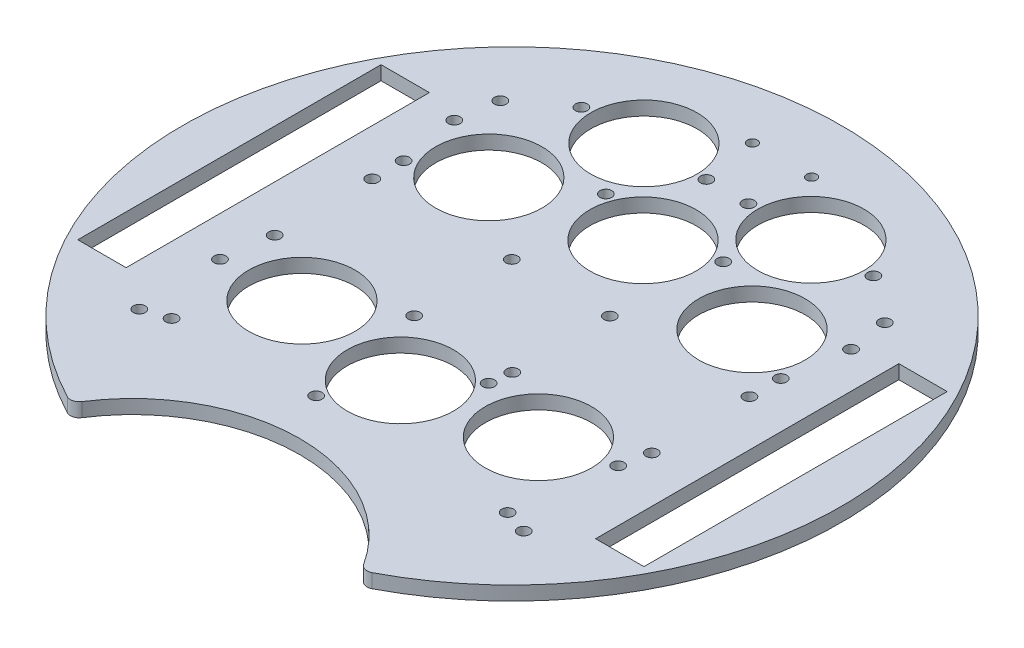
SolidWorks part; units mm, degrees
ref_plane "Front Plane" through (0, 0, 0) normal (0, 0, 1) x (1, 0, 0)
ref_plane "Top Plane" through (0, 0, 0) normal (0, 1, 0) x (1, 0, 0)
ref_plane "Right Plane" through (0, 0, 0) normal (1, 0, 0) x (0, 0, -1)
sketch "Sketch1" plane through (0, 0, 0) normal (0, 1, 0) x (1, 0, 0)
  line L0 (0, 0) -> (-43.7357, 41.0754) construction
  line L1 (0, 86.2583) -> (0, -96.8543) construction
  line L3 (-32.9956, -67.352) -> (0, -86.402) construction
  line L4 (32.9956, -67.352) -> (0, -86.402) construction
  line L5 (0, 0) -> (-13.6167, -50.8184) construction
  line L6 (55.5325, -36.9707) -> (45.152, -29.4289) construction
  line L7 (0, 0) -> (-48.2091, 57.4533) construction
  line L8 (-83.3992, 0) -> (107.0959, 0) construction
  line L9 (53.4101, -34.3971) -> (53.4101, 34.6029)
  line L10 (-64.4101, -34.3971) -> (-53.4101, -34.3971)
  line L11 (-64.4101, -34.3971) -> (-64.4101, 34.6029)
  line L12 (-64.4101, 34.6029) -> (-53.4101, 34.6029)
  line L13 (-53.4101, -34.3971) -> (-53.4101, 34.6029)
  line L14 (64.4101, 34.6029) -> (53.4101, 34.6029)
  line L15 (64.4101, -34.3971) -> (64.4101, 34.6029)
  line L16 (64.4101, -34.3971) -> (53.4101, -34.3971)
  line L17 (0, 0) -> (13.6167, -50.8184) construction
  line L18 (41.9192, -33.8784) -> (45.152, -29.4289) construction
  line L19 (0, 0) -> (48.2091, 57.4533) construction
  line L20 (52.2843, -41.4268) -> (41.9192, -33.8784) construction
  line L21 (64.9519, -37.5) -> (0, 0) construction
  line L22 (28.5723, -45.8735) -> (34.7503, -57.019) construction
  line L23 (28.5723, -45.8735) -> (23.7619, -48.54) construction
  line L24 (44.9916, 49.3407) -> (36.7843, 39.5596) construction
  line L25 (32.5711, 43.0949) -> (36.7843, 39.5596) construction
  line L26 (23.7619, -48.54) -> (29.9399, -59.6854) construction
  line L27 (-28.5723, -45.8735) -> (-34.7503, -57.019) construction
  line L28 (-23.7619, -48.54) -> (-29.9399, -59.6854) construction
  line L29 (-18.4555, -45.8919) -> (-23.0541, -33.9225) construction
  line L30 (-23.0541, -33.9225) -> (-17.92, -31.9499) construction
  line L31 (-28.5723, -45.8735) -> (-23.7619, -48.54) construction
  line L32 (-40.7784, 52.876) -> (-32.5711, 43.0949) construction
  line L33 (-32.5711, 43.0949) -> (-36.7843, 39.5596) construction
  line L34 (40.7784, 52.876) -> (32.5711, 43.0949) construction
  line L35 (-13.6167, -50.8184) -> (-25.1096, -20.9046) construction
  line L36 (-44.9916, 49.3407) -> (-36.7843, 39.5596) construction
  line L37 (-13.3214, -43.9193) -> (-17.92, -31.9499) construction
  line L38 (13.6167, -50.8184) -> (24.3327, -22.8079) construction
  line L39 (18.4555, -45.8919) -> (23.0541, -33.9225) construction
  line L40 (23.0541, -33.9225) -> (17.92, -31.9499) construction
  line L41 (13.3214, -43.9193) -> (17.92, -31.9499) construction
  line L42 (-58.5537, 0) -> (91.2411, 0) construction
  line L43 (-55.5325, -36.9707) -> (-45.152, -29.4289) construction
  line L44 (-52.2843, -41.4268) -> (-41.9192, -33.8784) construction
  line L45 (-41.9192, -33.8784) -> (-45.152, -29.4289) construction
  line L46 (0, 34.6626) -> (0, -51.647) construction
  line L47 (-37.1849, 0) -> (48.113, 0) construction
  line L48 (0, 49.2959) -> (0, -33.0158) construction
  line L54 (8.45, 45.0502) -> (-8.45, 71.1502) construction
  line L55 (8.45, 71.1502) -> (-8.45, 45.0502) construction
  arc A0 (32.9956, -67.352) -> (-32.9956, -67.352) centre (0, 0) ccw
  arc A1 (32.9956, -67.352) -> (-32.9956, -67.352) centre (0, -86.402) ccw
  circle A2 centre (0, 0) radius 74 construction
  arc A3 (56.3744, 49.4664) -> (44.9543, 49.2959) centre (50.737, 44.5198) ccw construction
  arc A4 (-56.3744, 49.4664) -> (-44.9543, 49.2959) centre (-50.737, 44.5198) cw construction
  arc A5 (-45.9, -59.3143) -> (-34.7503, -57.019) centre (-41.31, -53.3829) ccw construction
  arc A6 (45.9, -59.3143) -> (34.7503, -57.019) centre (41.31, -53.3829) cw construction
  arc A7 (-38.9256, 64.1077) -> (-40.7407, 52.8315) centre (-35.033, 57.6969) ccw construction
  arc A8 (-25.9781, -70.3572) -> (-29.9399, -59.6854) centre (-23.3803, -63.3215) cw construction
  arc A9 (25.9781, -70.3572) -> (29.9399, -59.6854) centre (23.3803, -63.3215) ccw construction
  arc A10 (38.9256, 64.1077) -> (40.7407, 52.8315) centre (35.033, 57.6969) cw construction
  arc A11 (53.2525, -52.8127) -> (52.2843, -41.4268) centre (47.9272, -47.5314) ccw construction
  arc A12 (66.658, -34.376) -> (55.5325, -36.9707) centre (59.9914, -30.9401) cw construction
  arc A13 (-5.2684, -48.6449) -> (-13.3214, -43.9193) centre (-6.3241, -41.2196) cw construction
  arc A14 (-21.2728, -54.7938) -> (-18.4555, -45.8919) centre (-25.4604, -48.5717) ccw construction
  arc A15 (-66.658, -34.376) -> (-55.5325, -36.9707) centre (-59.9914, -30.9401) ccw construction
  arc A16 (-53.2525, -52.8127) -> (-52.2843, -41.4268) centre (-47.9272, -47.5314) cw construction
  arc A17 (21.2728, -54.7938) -> (18.4555, -45.8919) centre (25.4604, -48.5717) cw construction
  arc A18 (5.2684, -48.6449) -> (13.3214, -43.9193) centre (6.3241, -41.2196) ccw construction
  circle A19 centre (-42.9101, 11.1) radius 1.35
  circle A20 centre (-42.9101, -11.1) radius 1.35
  circle A21 centre (-11.1601, -11.1) radius 1.35
  circle A22 centre (-11.1601, 11.1) radius 1.35
  circle A23 centre (11.1601, 11.1) radius 1.35
  circle A24 centre (11.1601, -11.1) radius 1.35
  circle A25 centre (42.9101, -11.1) radius 1.35
  circle A26 centre (42.9101, 11.1) radius 1.35
  circle A27 centre (26.9058, -20.9046) radius 12.095
  circle A28 centre (19, 49) radius 12.095
  circle A29 centre (0, 29.7936) radius 12.095
  circle A30 centre (0, -25.4092) radius 12.095
  circle A31 centre (29.9399, 24.6519) radius 12.095
  circle A32 centre (-26.9058, -20.9046) radius 12.095
  circle A33 centre (6.731, 61.4226) radius 1.143
  circle A34 centre (-6.731, 61.4226) radius 1.143
  arc A35 (-5.8539, 64.7449) -> (5.8576, 64.7385) centre (0, 61.4226) cw construction
  arc A36 (5.8576, 64.7385) -> (5.8576, 58.1067) centre (6.731, 61.4226) cw construction
  arc A37 (-5.8539, 58.1002) -> (-5.8539, 64.7449) centre (-6.731, 61.4226) cw construction
  arc A38 (5.8576, 58.1067) -> (-5.8539, 58.1002) centre (0, 61.4226) cw construction
  circle A39 centre (-29.9399, 24.6519) radius 12.095
  circle A40 centre (-33.218, 49) radius 1.35
  circle A41 centre (-4.782, 49) radius 1.35
  circle A42 centre (4.782, 49) radius 1.35
  circle A43 centre (-31.7919, 27.0969) radius 12.095 construction
  circle A44 centre (-42.9101, 18.2348) radius 1.35
  circle A45 centre (42.9101, 18.2348) radius 1.35
  circle A46 centre (-31.0383, -26.9744) radius 12.095 construction
  circle A47 centre (31.0383, -26.9744) radius 12.095 construction
  circle A48 centre (31.7919, 27.0969) radius 12.095 construction
  circle A49 centre (-19, 49) radius 12.095
  circle A50 centre (45.1387, 31.9972) radius 1.35
  circle A51 centre (-45.1387, 31.9972) radius 1.35
  circle A52 centre (13.3469, 34.6938) radius 1.35
  circle A53 centre (-6.5548, -38.0261) radius 1.35
  circle A54 centre (-31.7919, 27.0969) radius 14.218 construction
  circle A55 centre (-13.3469, 34.6938) radius 1.35
  circle A56 centre (10.597, -15.93) radius 1.35
  circle A57 centre (-38.2343, -39.237) radius 1.35
  circle A58 centre (0, 29.7936) radius 14.218 construction
  circle A59 centre (-43.7357, -41.0754) radius 1.35
  circle A60 centre (-43.7357, 41.0754) radius 1.35
  circle A61 centre (43.7357, -41.0754) radius 1.35
  circle A62 centre (31.7919, 27.0969) radius 14.218 construction
  circle A63 centre (33.218, 49) radius 1.35
  circle A64 centre (0, 0) radius 60 construction
  circle A66 centre (-19, 49) radius 14.218 construction
  circle A67 centre (43.7357, 41.0754) radius 1.35
  circle A70 centre (19, 49) radius 14.218 construction
  circle A71 centre (-44.3852, -22.0742) radius 1.35
  circle A74 centre (-31.0383, -26.9744) radius 14.218 construction
  circle A78 centre (0, -25.4092) radius 14.218 construction
  circle A80 centre (41.6017, -17.4578) radius 1.35
  circle A81 centre (38.2343, -39.237) radius 1.35
  circle A82 centre (31.0383, -26.9744) radius 14.218 construction
  point P14 (-62.6039, 0)
  point P23 (62.6039, 0)
  point P35 (-31.5178, -45.012)
  point P40 (-46.7211, -26.9744)
  point P45 (-34.6777, 41.3272)
  point P84 (-20.4871, -32.9362)
  point P154 (0, 58.1002)
  dimension "D1" = 150
  dimension "D2" = 76.2
  dimension "D10" = 148
  dimension "D13" = 2.7
  dimension "D14" = 2.7
  dimension "D22" = 2.286
  dimension "D20" = 2.7
  dimension "D27" = 2.7
  dimension "D28" = 2.7
  dimension "D3" = 120
  dimension "D4" = 69
  dimension "D5" = 11
  dimension "D9" = 30
  dimension "D16" = 5.5
  dimension "D7" = 5.5
  dimension "D8" = 12.8224
  dimension "D6" = 12.8224
  dimension "D11" = 5.5
  dimension "D12" = 5.5
  dimension "D17" = 22.2
  dimension "D19" = 22.2
  dimension "D15" = 10.5
  dimension "D18" = 31.75
  dimension "D23" = 13.462
  dimension "D24" = 16.9
  dimension "D25" = 26.1
  dimension "D21" = 38
  dimension "D26" = 49
extrude "Boss-Extrude2" add sketch "Sketch1" along normal blind 3.175
fillet "Fillet1" radius 2 2 edges at (-32.9956, 1.5875, 67.352) (32.9956, 1.5875, 67.352)
equation "\"D10@Sketch1\"=150-2"
